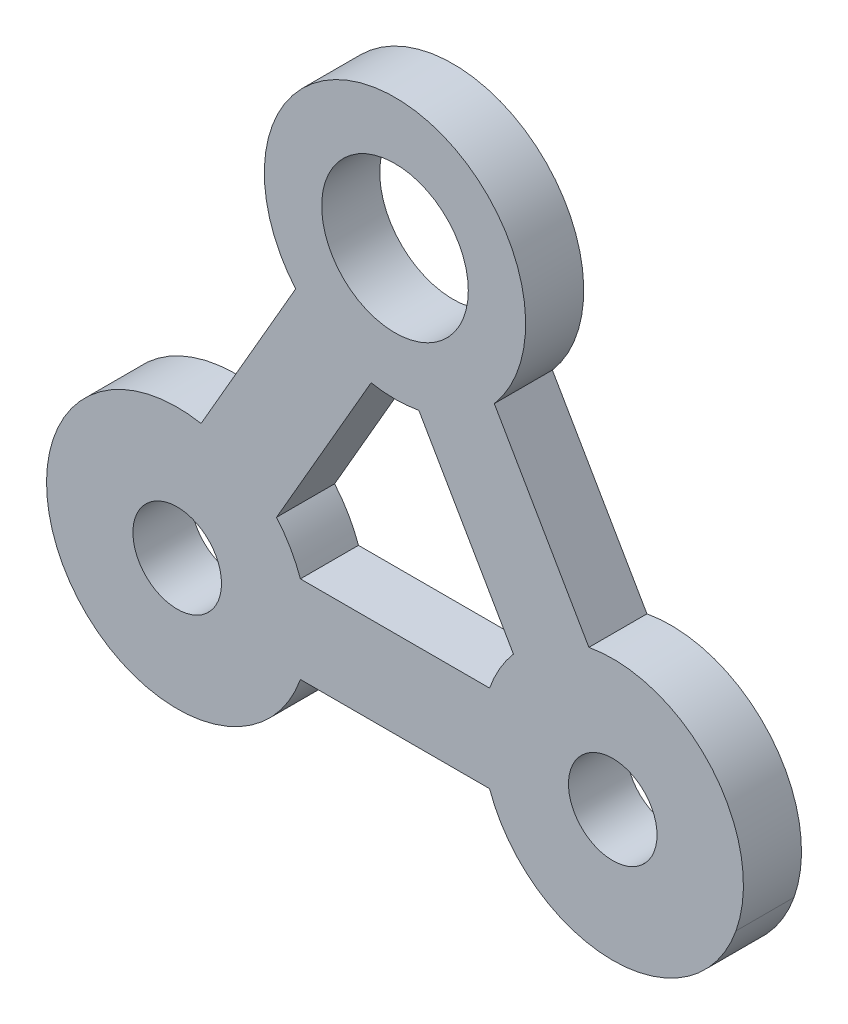
SolidWorks part; units mm, degrees
ref_plane "前视基准面" through (0, 0, 0) normal (0, 0, 1) x (1, 0, 0)
ref_plane "上视基准面" through (0, 0, 0) normal (0, 1, 0) x (1, 0, 0)
ref_plane "右视基准面" through (0, 0, 0) normal (1, 0, 0) x (0, 0, -1)
sketch "草图1" plane through (0, 0, 0) normal (0, 0, 1) x (1, 0, 0)
  line L0 (8.4244, -21.9438) -> (1.9097, -10.6599)
  line L1 (-11.7717, -10.6599) -> (-18.2864, -21.9437)
  line L2 (-27.71, -26.2658) -> (-27.7252, -26.2922)
  line L3 (-11.4457, -33.7922) -> (1.5837, -33.7922)
  line L4 (10.0443, -39.7922) -> (10.069, -39.7922)
  line L5 (-3.2864, -13.6599) -> (3.2283, -24.9438)
  line L6 (1.5837, -27.7922) -> (-11.4457, -27.7922)
  line L7 (-13.0903, -24.9437) -> (-6.5755, -13.6599)
  line L8 (-40.586, -4.8114) -> (37.2155, -4.8114) construction
  line L9 (-4.9309, 9.3813) -> (-4.9309, -20.8727) construction
  arc A0 (1.9097, -10.6599) -> (-11.7717, -10.6599) centre (-4.9309, -4.8114) ccw
  arc A1 (-18.2864, -21.9437) -> (-27.71, -26.2658) centre (-19.931, -30.7922) ccw
  arc A2 (-27.7252, -26.2922) -> (-26.7717, -36.6406) centre (-19.931, -30.7922) ccw
  arc A3 (-26.7717, -36.6406) -> (-11.4457, -33.7922) centre (-19.931, -30.7922) ccw
  arc A4 (1.5837, -33.7922) -> (10.0443, -39.7922) centre (10.069, -30.7922) ccw
  arc A5 (10.069, -39.7922) -> (18.5543, -33.7923) centre (10.069, -30.7922) ccw
  arc A6 (18.5543, -33.7923) -> (8.4244, -21.9438) centre (10.069, -30.7922) ccw
  circle A7 centre (10.069, -30.7922) radius 3.05
  arc A8 (3.2283, -24.9438) -> (1.5837, -27.7922) centre (10.069, -30.7922) ccw
  arc A9 (-11.4457, -27.7922) -> (-13.0903, -24.9437) centre (-19.931, -30.7922) ccw
  arc A10 (-6.5755, -13.6599) -> (-3.2864, -13.6599) centre (-4.9309, -4.8114) ccw
  circle A11 centre (-4.9309, -4.8114) radius 5.05
  circle A12 centre (-19.931, -30.7922) radius 3.05
  dimension "D1" = 6.1
  dimension "D4" = 10.1
  dimension "D5" = 6.1
  dimension "D2" = 4.8114
  dimension "D3" = 4.9309
extrude "凸台-拉伸1" add sketch "草图1" along normal blind 4
